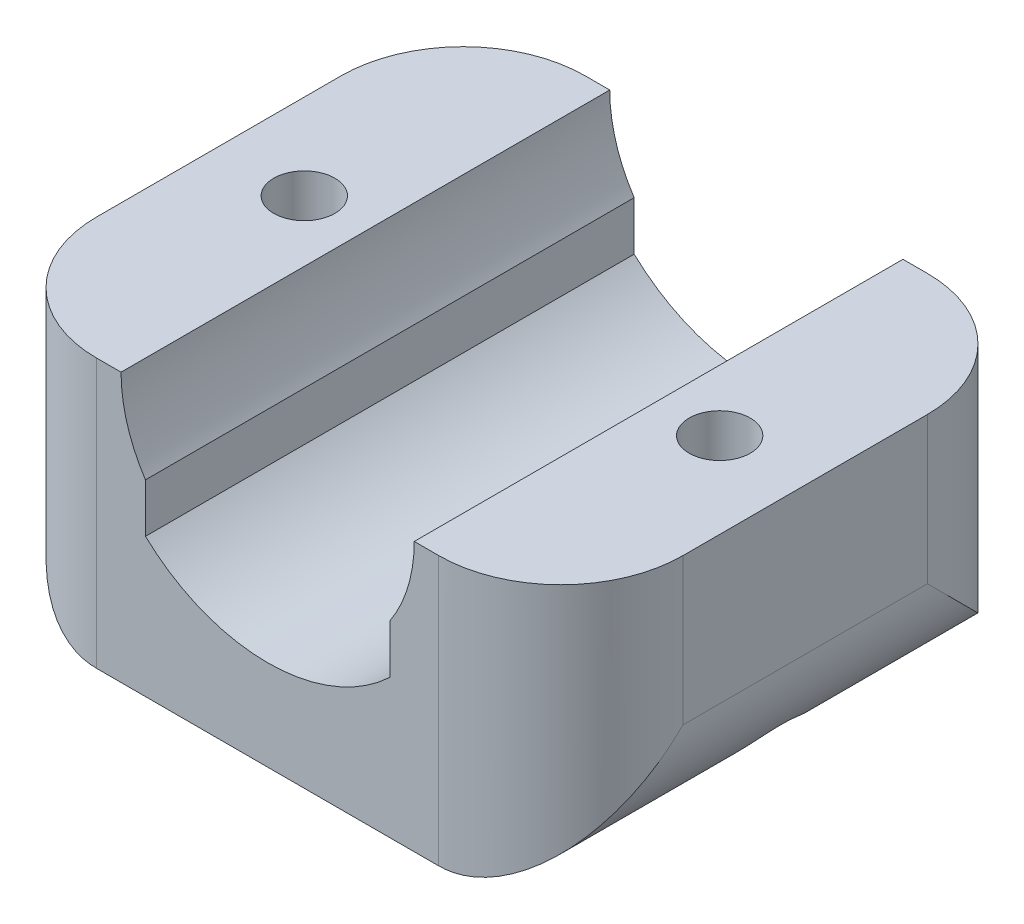
SolidWorks part; units mm, degrees
ref_plane "Front Plane" through (0, 0, 0) normal (0, 0, 1) x (1, 0, 0)
ref_plane "Top Plane" through (0, 0, 0) normal (0, 1, 0) x (1, 0, 0)
ref_plane "Right Plane" through (0, 0, 0) normal (1, 0, 0) x (0, 0, -1)
sketch "Sketch1" plane through (0, 0, 0) normal (0, 0, 1) x (1, 0, 0)
  line L0 (0, -6) -> (0, -11) construction
  line L1 (-12, 0) -> (12, 0)
  line L2 (-12, 0) -> (-12, -11)
  line L3 (-12, -11) -> (12, -11)
  line L4 (12, 0) -> (12, -11)
  circle A0 centre (0, 0) radius 6
  dimension "D1" = 12
  dimension "D2" = 24
  dimension "D3" = 5
extrude "Boss-Extrude1" add sketch "Sketch1" along normal mid plane 20 contours L0 A0 L1 L2 L3 | A0 L0 L3 L4 L1
sketch "Sketch2" plane through (0, 0, 0) normal (0, 0, 1) x (1, 0, 0)
  line L1 (-5, 0) -> (5, 0)
  line L2 (-5, 0) -> (-5, -5.3188)
  line L3 (-5, -5.3188) -> (5, -5.3188)
  line L4 (5, 0) -> (5, -5.3188)
  circle A0 centre (0, 0) radius 7.3
  arc A1 (-6, 0) -> (6, 0) centre (0, 0) ccw construction
  dimension "D1" = 1.3
  dimension "D2" = 10
extrude "Cut-Extrude1" cut sketch "Sketch2" against normal through all both and the other way through all contours L3 A0 | L4 L1 L2 L3
sketch "Sketch3" plane through (0, 0, 0) normal (0, 1, 0) x (1, 0, 0)
  line L0 (-8.5, 0) -> (8.5, 0) construction
  circle A0 centre (-8.5, 0) radius 1.25
  circle A1 centre (8.5, 0) radius 1.25
  dimension "D1" = 2.5
  dimension "D2" = 17
extrude "Cut-Extrude2" cut sketch "Sketch3" against normal blind 17
fillet "Fillet1" radius 5 4 edges at (12, -5.5, -10) (-12, -5.5, -10) (12, -5.5, 10) (-12, -5.5, 10)
sketch "Sketch4" plane through (0, 0, 0) normal (0, 0, 1) x (1, 0, 0)
  line L0 (12, -6) -> (12, -11)
  line L1 (12, 0) -> (-12, 0)
  line L2 (12, 0) -> (12, -6)
  line L3 (7, -11) -> (-7, -11)
  line L4 (-12, 0) -> (-12, -6)
  line L5 (12, -11) -> (7, -11)
  line L6 (-12, -6) -> (-12, -11)
  line L7 (-12, -11) -> (-7, -11)
  arc A0 (7, -11) -> (12, -6) centre (7, -6) ccw
  arc A1 (-12, -6) -> (-7, -11) centre (-7, -6) ccw
  point P10 (-12, -11)
  dimension "D1" = 5
  dimension "D2" = 5
extrude "Cut-Extrude3" cut sketch "Sketch4" against normal through all both and the other way through all contours A0 L5 L0 | A1 L6 L7
sketch "Sketch5" plane through (0, -11, 0) normal (0, -1, 0) x (1, 0, 0)
  circle A0 centre (-8.5, 0) radius 2.5
  circle A1 centre (8.5, 0) radius 2.5
  dimension "D1" = 5
extrude "Cut-Extrude4" cut sketch "Sketch5" against normal blind 6
